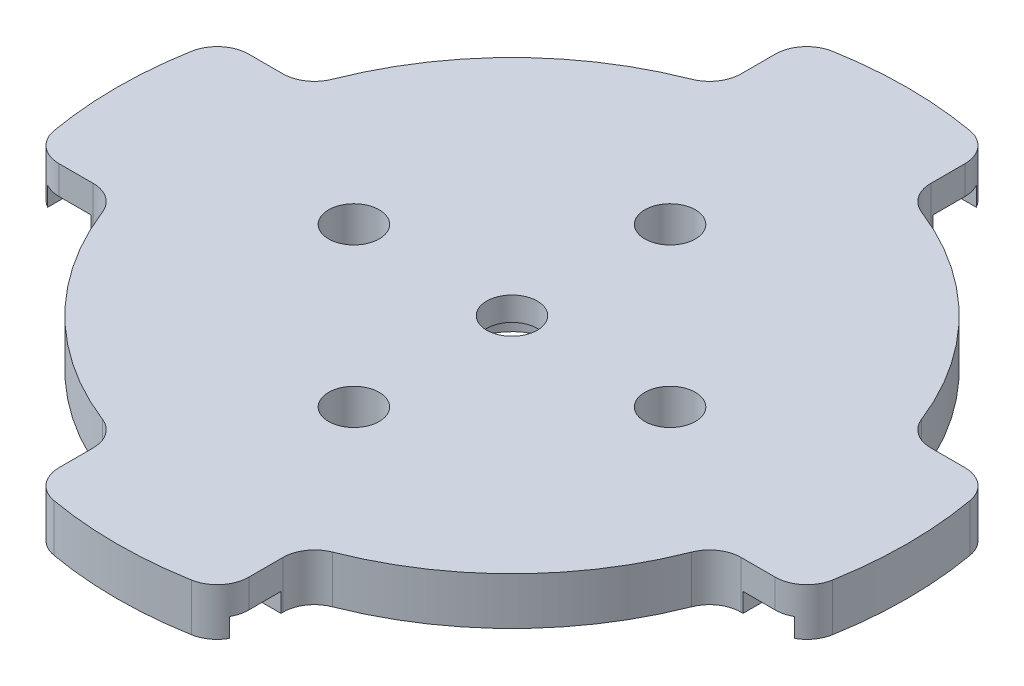
SolidWorks part; units mm, degrees
material "A-Glasfaser"
ref_plane "Ebene vorne" through (0, 0, 0) normal (0, 0, 1) x (1, 0, 0)
ref_plane "Ebene oben" through (0, 0, 0) normal (0, 1, 0) x (1, 0, 0)
ref_plane "Ebene rechts" through (0, 0, 0) normal (1, 0, 0) x (0, 0, -1)
sketch "Skizze1" plane through (0, 0, 0) normal (0, 1, 0) x (1, 0, 0)
  line L0 (-6, 20.4939) -> (-6, 22.6495)
  line L1 (6, 20.4939) -> (6, 22.6495)
  line L3 (0, 25) -> (0, 23.9906) construction
  line L4 (-6, 20.4939) -> (6, 20.4939) construction
  line L5 (20.4939, -6) -> (22.6495, -6)
  line L6 (20.4939, 6) -> (22.6495, 6)
  line L7 (25, 0) -> (0, 0) construction
  line L8 (-6, -20.4939) -> (-6, -22.6495)
  line L9 (6, -20.4939) -> (6, -22.6495)
  line L10 (0, -25) -> (0, 0) construction
  line L11 (-20.4939, 6) -> (-22.6495, 6)
  line L12 (-20.4939, -6) -> (-22.6495, -6)
  line L13 (-25, 0) -> (0, 0) construction
  line L14 (0, 10) -> (-10, 0) construction
  line L15 (-10, 0) -> (0, -10) construction
  line L16 (0, -10) -> (10, 0) construction
  line L17 (10, 0) -> (0, 10) construction
  line L18 (0, 22.3906) -> (0, 0) construction
  circle A0 centre (0, 0) radius 19
  arc A1 (-7.2727, 18.6308) -> (-18.6308, 7.2727) centre (0, 0) ccw
  circle A2 centre (0, 0) radius 1.6
  arc A3 (4.3478, 24.619) -> (-4.3478, 24.619) centre (0, 0) ccw
  arc A4 (-6, 22.6495) -> (-4.3478, 24.619) centre (-4, 22.6495) cw
  arc A5 (-6, 20.4939) -> (-7.2727, 18.6308) centre (-8, 20.4939) cw
  arc A6 (6, 22.6495) -> (4.3478, 24.619) centre (4, 22.6495) ccw
  arc A7 (6, 20.4939) -> (7.2727, 18.6308) centre (8, 20.4939) ccw
  arc A8 (20.4939, -6) -> (18.6308, -7.2727) centre (20.4939, -8) ccw
  arc A9 (22.6495, -6) -> (24.619, -4.3478) centre (22.6495, -4) ccw
  arc A10 (24.619, -4.3478) -> (24.619, 4.3478) centre (0, 0) ccw
  arc A11 (22.6495, 6) -> (24.619, 4.3478) centre (22.6495, 4) cw
  arc A12 (20.4939, 6) -> (18.6308, 7.2727) centre (20.4939, 8) cw
  arc A13 (-6, -20.4939) -> (-7.2727, -18.6308) centre (-8, -20.4939) ccw
  arc A14 (-6, -22.6495) -> (-4.3478, -24.619) centre (-4, -22.6495) ccw
  arc A15 (-4.3478, -24.619) -> (4.3478, -24.619) centre (0, 0) ccw
  arc A16 (6, -22.6495) -> (4.3478, -24.619) centre (4, -22.6495) cw
  arc A17 (6, -20.4939) -> (7.2727, -18.6308) centre (8, -20.4939) cw
  arc A18 (-20.4939, 6) -> (-18.6308, 7.2727) centre (-20.4939, 8) ccw
  arc A19 (-22.6495, 6) -> (-24.619, 4.3478) centre (-22.6495, 4) ccw
  arc A20 (-24.619, 4.3478) -> (-24.619, -4.3478) centre (0, 0) ccw
  arc A21 (-22.6495, -6) -> (-24.619, -4.3478) centre (-22.6495, -4) cw
  arc A22 (-20.4939, -6) -> (-18.6308, -7.2727) centre (-20.4939, -8) cw
  circle A23 centre (0, 10) radius 1.6
  circle A24 centre (10, 0) radius 1.6
  circle A25 centre (-10, 0) radius 1.6
  circle A26 centre (0, -10) radius 1.6
  arc A27 (-18.6308, -7.2727) -> (-7.2727, -18.6308) centre (0, 0) ccw
  arc A28 (18.6308, 7.2727) -> (7.2727, 18.6308) centre (0, 0) ccw
  arc A29 (7.2727, -18.6308) -> (18.6308, -7.2727) centre (0, 0) ccw
  point P20 (0, 20.4939)
  point P68 (-6, 21.5717)
  dimension "D1" = 40
  dimension "D2" = 38
  dimension "D3" = 3.2
  dimension "D4" = 50
  dimension "D5" = 2
  dimension "D6" = 12
  dimension "D8" = 10
  dimension "D7" = 4
extrude "Aufsatz-Linear austragen1" add sketch "Skizze1" along normal blind 3 contours A0 A26 A25 A24 A23 A2 | A17 A29 A8 L5 A9 A10 A11 L6 A12 A28 A7 L1 A6 A3 A4 L0 A5 A1 A18 L11 A19 A20 A21 L12 A22 A27 A13 L8 A14 A15 A16 L9 A0
sketch "Skizze6" plane through (0, 0, 0) normal (0, -1, 0) x (1, 0, 0)
  circle A0 centre (0, 0) radius 3
  dimension "D1" = 6
extrude "Schnitt-Linear austragen2" cut sketch "Skizze6" against normal blind 1.5
sketch "Skizze7" plane through (0, 0, 0) normal (0, -1, 0) x (1, 0, 0)
  line L0 (-20.4939, -6) -> (-22.6495, -6) construction
  line L1 (-23.619, 6) -> (-20.619, 6)
  line L2 (-23.619, 6) -> (-23.619, -6)
  line L3 (-23.619, -6) -> (-20.619, -6)
  line L4 (-20.619, 6) -> (-20.619, -6)
  line L5 (-20.4939, 6) -> (-22.6495, 6) construction
  line L6 (6, 23.619) -> (6, 20.619)
  line L7 (6, 23.619) -> (-6, 23.619)
  line L8 (6, 20.619) -> (-6, 20.619)
  line L9 (-6, 23.619) -> (-6, 20.619)
  line L10 (23.619, -6) -> (20.619, -6)
  line L11 (23.619, -6) -> (23.619, 6)
  line L12 (20.619, -6) -> (20.619, 6)
  line L13 (23.619, 6) -> (20.619, 6)
  line L14 (-6, -23.619) -> (-6, -20.619)
  line L15 (-6, -23.619) -> (6, -23.619)
  line L16 (-6, -20.619) -> (6, -20.619)
  line L17 (6, -23.619) -> (6, -20.619)
  point P24 (0, 0)
  dimension "D1" = 1
  dimension "D2" = 3
  dimension "D3" = 0
  dimension "D4" = 0
  dimension "D6" = 0
  dimension "D5" = 4
extrude "Schnitt-Linear austragen3" cut sketch "Skizze7" against normal blind 1.2
